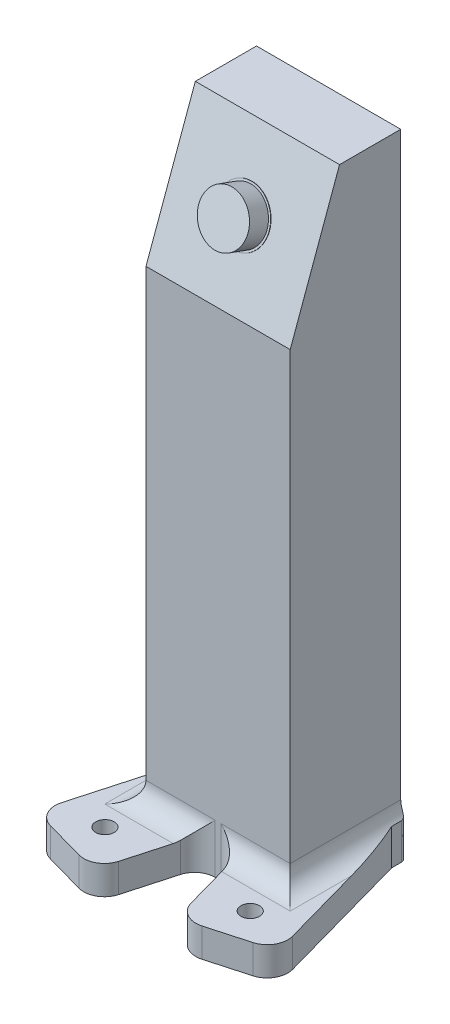
SolidWorks part; units mm, degrees
ref_plane "Ebene vorne" through (0, 0, 0) normal (0, 0, 1) x (1, 0, 0)
ref_plane "Ebene oben" through (0, 0, 0) normal (0, 1, 0) x (1, 0, 0)
ref_plane "Ebene rechts" through (0, 0, 0) normal (1, 0, 0) x (0, 0, -1)
sketch "Skizze1" plane through (0, 0, 0) normal (1, 0, 0) x (0, 0, -1)
  line L0 (0, 0) -> (11.9707, 0)
  line L1 (0, 0) -> (0, 120)
  line L2 (0, 120) -> (11.9707, 152.8892)
  line L3 (11.9707, 152.8892) -> (11.9707, 0) construction
  line L4 (11.9707, 0) -> (26.82, 0)
  line L5 (26.82, 0) -> (26.82, 152.8892)
  line L6 (26.82, 152.8892) -> (11.9707, 152.8892)
  dimension "D1" = 70
  dimension "D2" = 120
  dimension "D3" = 35
  dimension "D4" = 26.82
extrude "Aufsatz-Linear austragen1" add sketch "Skizze1" along normal blind 35
sketch "Skizze3" plane through (0, 14.0373, 38.5673) normal (0, 0.342, 0.9397) x (1, 0, 0)
  line L0 (0, 147.7631) -> (35, 112.7631) construction
  line L1 (17.5, 130.2631) -> (35, 147.7631) construction
  line L2 (35, 147.7631) -> (0, 147.7631) construction
  line L3 (35, 147.7631) -> (35, 112.7631) construction
  circle A0 centre (17.5, 130.2631) radius 6
  dimension "D1" = 12
extrude "Aufsatz-Linear austragen2" add sketch "Skizze3" along normal blind 5
sketch "Skizze4" plane through (0, 14.0373, 38.5673) normal (0, 0.342, 0.9397) x (1, 0, 0)
  circle A0 centre (17.5, 130.2631) radius 6.5
  dimension "D1" = 13
extrude "Aufsatz-Linear austragen3" add sketch "Skizze4" along normal blind 0.1
ref_plane "Ebene1" through (0, 120, 0) normal (0, -1, 0) x (-1, 0, 0)
ref_plane "Ebene2" through (0, 4.5, 0) normal (0, 1, 0) x (1, 0, 0)
sketch "Skizze7" plane through (0, 4.5, 0) normal (0, -1, 0) x (-1, 0, 0)
  line L0 (-35, 26.82) -> (0, 26.82) construction
  line L1 (-35, 0) -> (0, 26.82) construction
  line L2 (-17.5, 13.41) -> (-17.5, 26.82) construction
  line L4 (-17.5, 13.41) -> (-35, 13.41) construction
  line L5 (-35, 0) -> (-35, 26.82) construction
  circle A0 centre (-28.5, 5) radius 2.85
  circle A1 centre (-6.5, 5) radius 2.85
  circle A2 centre (-6.5, 21.82) radius 2.85
  circle A3 centre (-28.5, 21.82) radius 2.85
  dimension "D1" = 5.7
  dimension "D2" = 11
  dimension "D3" = 5
extrude "Schnitt-Linear austragen1" [suppressed] cut sketch "Skizze7" against normal through all
hole_wizard "Ø3.4 (3.4) Durchmesser Bohrung1" [suppressed] positions "3D-Skizze3" profile "Skizze8" hole size "Ø3.4" standard "DIN"
sketch3d "3D-Skizze3" [suppressed]
  line L0 (6.5, 101.5966, -5) -> (6.5, 4.5, -5) construction
  line L1 (6.5, 118.3109, -21.82) -> (6.5, 4.5, -21.82) construction
  line L2 (28.5, 118.3109, -21.82) -> (28.5, 4.5, -21.82) construction
  line L3 (28.5, 101.5966, -5) -> (28.5, 4.5, -5) construction
  point P0 (6.5, 4.5, -5)
  point P4 (6.5, 4.5, -21.82)
  point P8 (28.5, 4.5, -21.82)
  point P12 (28.5, 4.5, -5)
sketch "Skizze8" plane through (6.5, 4.5, -5) normal (1, 0, 0) x (0, 0, 1)
  line L0 (0, 0) -> (0, 4.5)
  line L1 (0, 4.5) -> (1.7, 4.5)
  line L2 (1.7, 4.5) -> (1.7, 0)
  line L5 (1.7, 0) -> (0, 0)
  line L11 (0, -6.35) -> (0, 107.95) construction
  dimension "Bohrerdurchmesser" = 3.4
  dimension "Bohrungstiefe" = 4.5
sketch "Skizze9" plane through (0, 0, 0) normal (0, -1, 0) x (1, 0, 0)
  circle A0 centre (17.4988, -21.6442) radius 1.425
  dimension "D1" = 2.85
extrude "Schnitt-Linear austragen2" cut sketch "Skizze9" against normal blind 10
sketch "Skizze10" plane through (0, 0, 0) normal (0, -1, 0) x (1, 0, 0)
  line L0 (35, -26.82) -> (36.2227, -26.82)
  line L1 (36.2227, -26.82) -> (36.2227, -23.3967)
  line L2 (36.2227, -23.3967) -> (46.8899, 14.7774)
  line L3 (117.4988, 267.461) -> (36.7609, -21.4705) construction
  line L4 (46.8899, 14.7774) -> (27.6278, 20.1599)
  line L5 (98.2367, 272.8435) -> (17.4988, -16.088) construction
  line L6 (27.6278, 20.1599) -> (21.9944, 0)
  line L7 (35, 0) -> (0, 0) construction
  line L8 (21.9944, 0) -> (35, -26.82)
  line L9 (17.5, 0) -> (17.5, -4.1312) construction
  line L10 (-1.2227, -26.82) -> (-1.2227, -23.3967)
  line L11 (0, -26.82) -> (-1.2227, -26.82)
  line L12 (13.0056, 0) -> (0, -26.82)
  line L13 (-1.2227, -23.3967) -> (-11.8899, 14.7774)
  line L14 (7.3722, 20.1599) -> (13.0056, 0)
  line L15 (-11.8899, 14.7774) -> (7.3722, 20.1599)
  line L16 (25.4933, 12.5213) -> (44.7554, 7.1388) construction
  circle A0 centre (35.1244, 9.83) radius 2.25
  circle A1 centre (-0.1244, 9.83) radius 2.25
  dimension "D1" = 4.5
extrude "Aufsatz-Linear austragen4" add sketch "Skizze10" against normal blind 7
fillet "Verrundung1" radius 5 10 edges at (6.5028, 7, 0) (28.4972, 7, 0) (35, 7, -13.41) (0, 7, -13.41) (-11.8899, 3.5, 14.7774) (7.3722, 3.5, 20.1599) (46.8899, 3.5, 14.7774) (27.6278, 3.5, 20.1599) (21.9944, 3.5, 0) (13.0056, 3.5, 0)
fillet "Verrundung2" radius 1 2 edges at (-1.2227, 4.362, -26.82) (36.2227, 4.362, -26.82)
